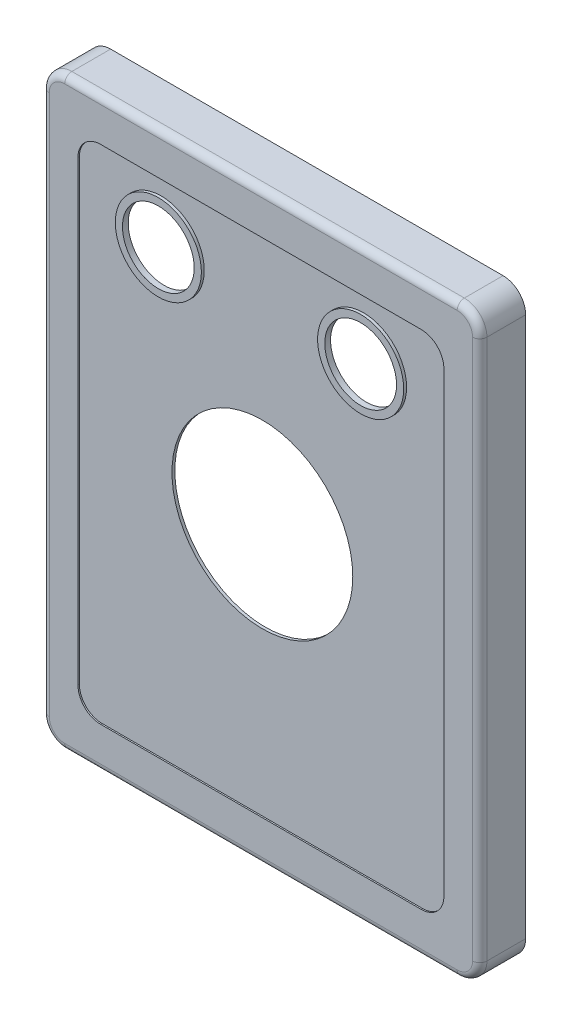
SolidWorks part; units mm, degrees
material "Nickel"
ref_plane "Front Plane" through (0, 0, 0) normal (0, 0, 1) x (1, 0, 0)
ref_plane "Top Plane" through (0, 0, 0) normal (0, 1, 0) x (1, 0, 0)
ref_plane "Right Plane" through (0, 0, 0) normal (1, 0, 0) x (0, 0, -1)
sketch "Sketch1" plane through (0, 0, 0) normal (0, 0, 1) x (1, 0, 0)
  line L1 (34.735, -51.816) -> (-34.735, -51.816)
  line L2 (38.735, -47.816) -> (38.735, 47.816)
  line L3 (34.735, 51.816) -> (-34.735, 51.816)
  line L4 (-38.735, -47.816) -> (-38.735, 47.816)
  line L5 (38.735, -51.816) -> (-38.735, 51.816) construction
  line L6 (38.735, 51.816) -> (-38.735, -51.816) construction
  arc A0 (-38.735, -47.816) -> (-34.735, -51.816) centre (-34.735, -47.816) ccw
  arc A1 (34.735, -51.816) -> (38.735, -47.816) centre (34.735, -47.816) ccw
  arc A2 (38.735, 47.816) -> (34.735, 51.816) centre (34.735, 47.816) ccw
  arc A3 (-34.735, 51.816) -> (-38.735, 47.816) centre (-34.735, 47.816) ccw
  point P0 (0, 0)
  dimension "D3" = 4
  dimension "D1" = 103.632
  dimension "D2" = 77.47
extrude "Boss-Extrude1" add sketch "Sketch1" against normal blind 8.128
sketch "Sketch3" plane through (0, 0, 0) normal (0, 0, 1) x (1, 0, 0)
  line L1 (-28.385, -44.45) -> (28.385, -44.45)
  line L2 (-32.385, -40.45) -> (-32.385, 40.45)
  line L3 (-28.385, 44.45) -> (28.385, 44.45)
  line L4 (32.385, -40.45) -> (32.385, 40.45)
  line L5 (-32.385, -44.45) -> (32.385, 44.45) construction
  line L6 (-32.385, 44.45) -> (32.385, -44.45) construction
  arc A0 (-32.385, -40.45) -> (-28.385, -44.45) centre (-28.385, -40.45) ccw
  arc A1 (28.385, -44.45) -> (32.385, -40.45) centre (28.385, -40.45) ccw
  arc A2 (32.385, 40.45) -> (28.385, 44.45) centre (28.385, 40.45) ccw
  arc A3 (-28.385, 44.45) -> (-32.385, 40.45) centre (-28.385, 40.45) ccw
  point P0 (0, 0)
  dimension "D3" = 4
  dimension "D4" = 4
  dimension "D1" = 88.9
  dimension "D2" = 64.77
extrude "Cut-Extrude1" cut sketch "Sketch3" against normal blind 0.254
sketch "Sketch4" plane through (0, 0, -0.254) normal (0, 0, 1) x (1, 0, 0)
  line L0 (-38.735, -47.816) -> (38.735, -47.816) construction
  line L1 (-34.735, -51.816) -> (34.735, -51.816) construction
  line L2 (28.385, 44.45) -> (-28.385, 44.45) construction
  line L3 (34.735, 51.816) -> (-34.735, 51.816) construction
  line L4 (32.385, -40.45) -> (32.385, 40.45) construction
  line L5 (-28.385, -44.45) -> (28.385, -44.45) construction
  line L22 (-17.907, 34.036) -> (17.907, 34.036) construction
  line L23 (-32.385, 40.45) -> (-32.385, -40.45) construction
  circle A0 centre (0, 0.254) radius 16.002
  circle A1 centre (17.907, 34.036) radius 6.35
  circle A2 centre (-17.907, 34.036) radius 6.35
  point P2 (0, 34.036)
  point P7 (0, -47.816)
  dimension "D1" = 32.004
  dimension "D3" = 12.7
  dimension "D5" = 17.78
  dimension "D2" = 52.07
  dimension "D4" = 35.814
  dimension "D6" = 10.414
  dimension "D7" = 17.78
  dimension "D8" = 14.478
  dimension "D9" = 44.704
  dimension "D10" = 32.385
fillet "Fillet3" radius 1.27 8 edges at (37.5634, -50.6444, 0) (0, -51.816, 0) (-37.5634, -50.6444, 0) (-38.735, 0, 0) (-37.5634, 50.6444, 0) (0, 51.816, 0) (37.5634, 50.6444, 0) (38.735, 0, 0)
shell "Shell2" thickness 0.508
extrude "Cut-Extrude3" cut sketch "Sketch4" against normal through all
sketch "Sketch6" plane through (0, 0, -0.254) normal (0, 0, 1) x (1, 0, 0)
  circle A0 centre (-17.907, 34.036) radius 6.35
  circle A1 centre (-17.907, 34.036) radius 7.62
  circle A2 centre (17.907, 34.036) radius 6.35
  circle A3 centre (17.907, 34.036) radius 7.62
  dimension "D1" = 15.24
  dimension "D2" = 15.24
extrude "Boss-Extrude5" add sketch "Sketch6" along normal blind 0.508
